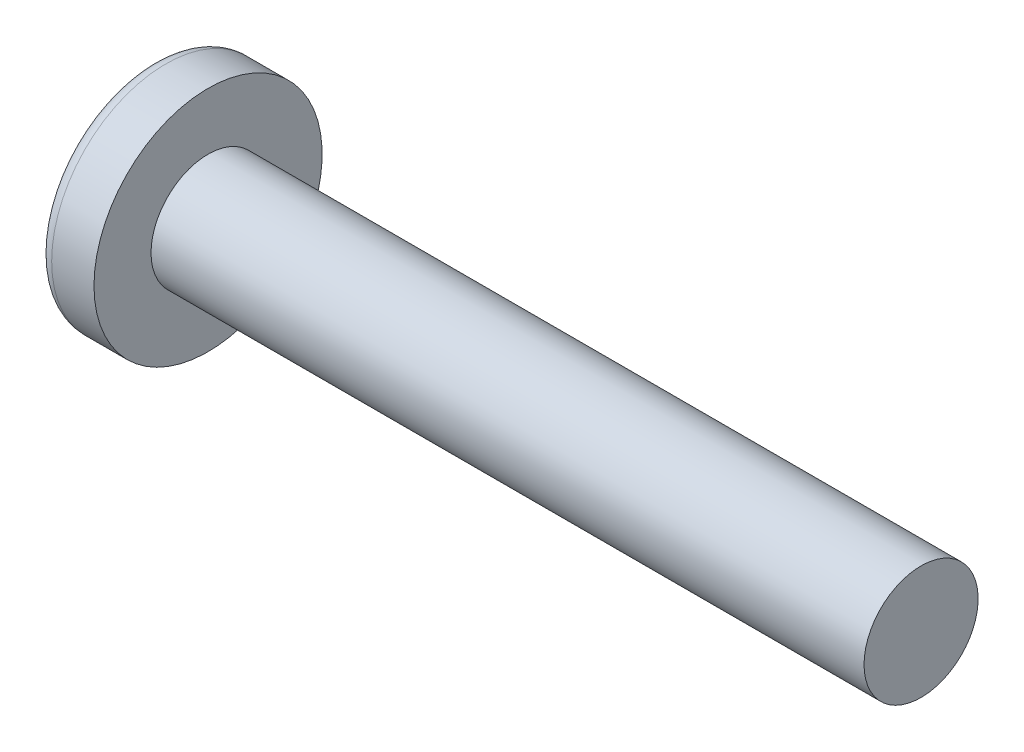
SolidWorks part; units mm, degrees
ref_plane "Plane1" through (0, 0, 0) normal (0, 0, 1) x (1, 0, 0)
ref_plane "Plane2" through (0, 0, 0) normal (0, 1, 0) x (1, 0, 0)
ref_plane "Plane3" through (0, 0, 0) normal (1, 0, 0) x (0, 0, -1)
other "Configuration Table"
sketch "BodySke" plane through (0, 0, 0) normal (0, 0, 1) x (1, 0, 0)
  line L0 (3.1, 2) -> (3.1, 4)
  line L1 (3.8, 6.35) -> (3.8, -3.175) construction
  line L2 (-25.4, 0) -> (127, 0) construction
  line L3 (28.1, 0) -> (0, 0)
  line L4 (3.1, 2) -> (28.1, 2)
  line L5 (28.1, 2) -> (28.1, 0)
  line L6 (1.6164, 4) -> (3.1, 4)
  line L7 (3.1, -2) -> (28.1, -2) construction
  line L8 (3.1, 6.35) -> (3.1, -3.175) construction
  arc A0 (1.227, 3.8007) -> (0, 0) centre (6.5, 0) ccw
  arc A2 (1.227, 3.8007) -> (1.6164, 4) centre (1.6164, 3.52) cw
  dimension "Head_crown_rad" = 6.5
  dimension "Head_fillet_rad" = 0.48
  dimension "Diameter" = 4
  dimension "Length" = 25
  dimension "Head_ht" = 3.1
  dimension "Head_dia" = 8
  dimension "Advance" = 0.7
  dimension "Thread_nom" = 25
revolve "Base-Revolve" add sketch "BodySke" angle 360 about L2
cosmetic thread "ThreadCosmetic" [suppressed] parameters "Thread_length"=24.3, "Thread_minor"=3.22
sketch "Sketch3" plane through (0, 0, 0) normal (1, 0, 0) x (0, 0, -1)
  line L0 (0.465, -2.2) -> (-0.465, -2.2)
  line L1 (0.465, -2.2) -> (0.465, 2.2)
  line L2 (-0.465, 2.2) -> (0.465, 2.2)
  line L3 (-0.465, 2.2) -> (-0.465, -2.2)
  dimension "Cross_dia" = 4.4
  dimension "D1" = 2.2
  dimension "Cross_width" = 0.93
  dimension "D2" = 0.465
ref_plane "Plane4" through (2.45, 0, 0) normal (1, 0, 0) x (0, 0, -1)
sketch "Sketch4" plane through (2.45, 0, 0) normal (1, 0, 0) x (0, 0, -1)
  line L0 (0.2325, -0.2325) -> (-0.2325, -0.2325)
  line L1 (0.2325, -0.2325) -> (0.2325, 0.2325)
  line L2 (-0.2325, 0.2325) -> (0.2325, 0.2325)
  line L3 (-0.2325, 0.2325) -> (-0.2325, -0.2325)
  dimension "D2" = 0.465
  dimension "D1" = 0.465
  dimension "D3" = 0.2325
  dimension "D4" = 0.2325
loft "Cut-Loft1" cut profiles "Sketch3", "Sketch4"
pattern_circular "CirPattern1" count 2 every 90 about axis through (0, 0, 0) along (1, 0, 0) of "Cut-Loft1"
sketch "ThdSchSke" plane through (0, 0, 0) normal (0, 0, 1) x (1, 0, 0)
  line L0 (3.8, -1.61) -> (3.5269, -2)
  line L1 (3.8, -1.61) -> (4.0731, -2)
  line L2 (4.0731, -2) -> (4.0731, -2.5)
  line L3 (-3.175, 0) -> (5.1513, 0) construction
  line L5 (4.0731, -2.5) -> (3.5269, -2.5)
  line L6 (3.5269, -2.5) -> (3.5269, -2)
  dimension "Diameter" = 4
  dimension "SideAngle" = 55
  dimension "VeeAngle" = 70
  dimension "Thread_minor" = 3.22
  dimension "Overcut" = 5
  dimension "Start" = 3.8
revolve "ThreadSchematic" [suppressed] cut sketch "ThdSchSke" angle 360 about L3
pattern_linear "ThdSchPat" [suppressed]
equation "\"D1@Sketch3\" = \"Cross_dia@Sketch3\" / 2"
equation "\"D2@Sketch3\" = \"Cross_width@Sketch3\" / 2"
equation "\"D1@Sketch4\" = \"Cross_width@Sketch3\" *.5"
equation "\"D2@Sketch4\" = \"D1@Sketch4\""
equation "\"D3@Sketch4\" = \"D1@Sketch4\" / 2"
equation "\"D4@Sketch4\" = \"D2@Sketch4\" / 2"
equation "\"Thread_length@ThreadCosmetic\" = ((sgn( (\"Length@BodySke\" - \"Advance@BodySke\" ) - \"Thread_nom@BodySke\" )-1)*( (\"Length@BodySke\" - \"Advance@BodySke\" ) - \"Thread_nom@BodySke\" ))/-2+ \"Thread_nom@BodySke\""
equation "\"Thread_minor@ThdSchSke\" = \"Thread_minor@ThreadCosmetic\""
equation "\"Diameter@ThdSchSke\" = \"Diameter@BodySke\""
equation "\"Overcut@ThdSchSke\" = \"Diameter@BodySke\" * 1.25"
equation "\"Start@ThdSchSke\" = \"Head_ht@BodySke\" + \"Length@BodySke\" - \"Thread_length@ThreadCosmetic\"  '---Non-countersunk---"
equation "\"Num_threads@ThdSchPat\" = int( \"Thread_length@ThreadCosmetic\" / \"Advance@BodySke\" + 0.999 )  + 1"
equation "\"Advance@ThdSchPat\" = \"Thread_length@ThreadCosmetic\" /  (\"Num_threads@ThdSchPat\" - 1) 'relax it"
